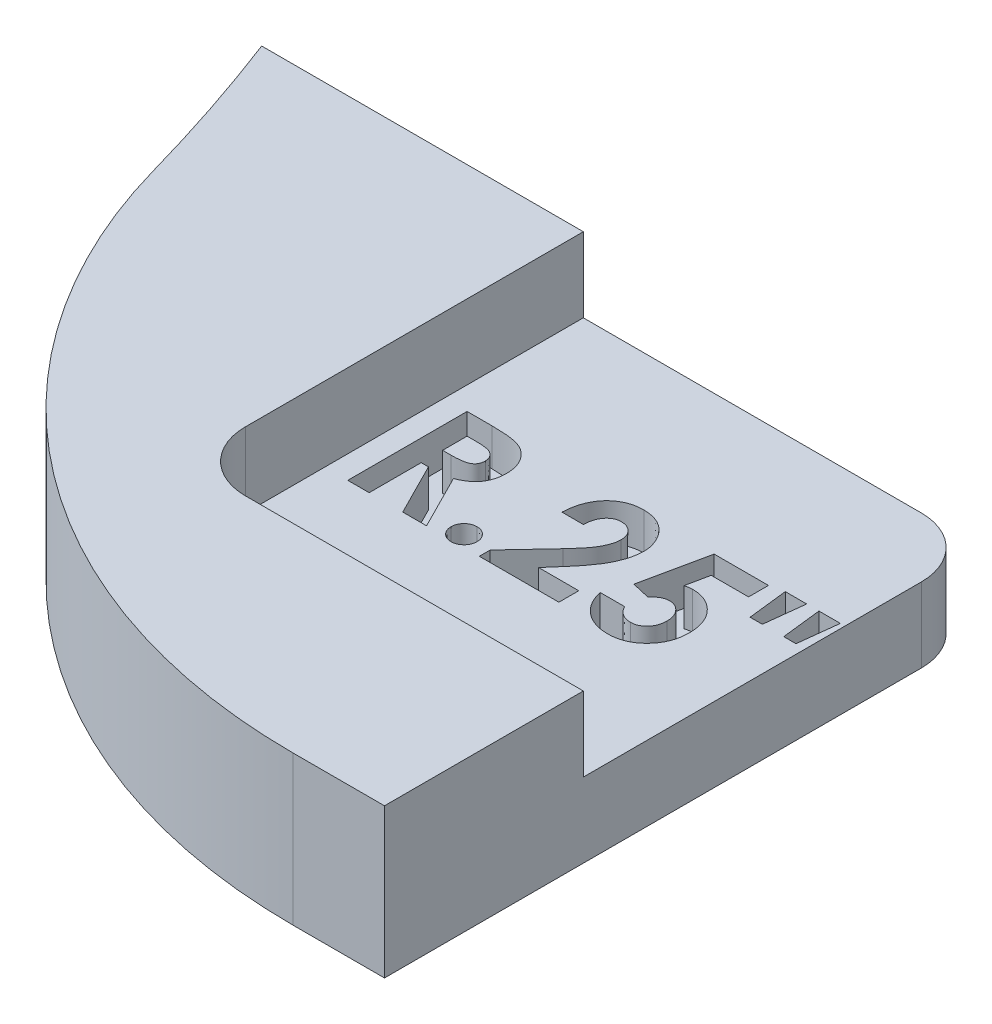
SolidWorks part; units mm, degrees
ref_plane "Front Plane" through (0, 0, 0) normal (0, 0, 1) x (1, 0, 0)
ref_plane "Top Plane" through (0, 0, 0) normal (0, 1, 0) x (1, 0, 0)
ref_plane "Right Plane" through (0, 0, 0) normal (1, 0, 0) x (0, 0, -1)
sketch "Sketch2" plane through (0, 0, 0) normal (0, 1, 0) x (1, 0, 0)
  line L0 (39.9034, 0) -> (66.5271, 0) construction
  line L4 (39.8718, 1.5875) -> (52.5718, 1.5875)
  line L5 (52.5718, 1.5875) -> (52.5718, 14.2875)
  line L6 (52.5718, 14.2875) -> (37.2579, 14.2875)
  arc A0 (39.8718, 1.5875) -> (37.2579, 14.2875) centre (0, 0) ccw
  arc A1 (37.2579, 14.2875) -> (-39.9034, 0) centre (0, 0) ccw construction
  arc A2 (-39.9034, 0) -> (39.9034, 0) centre (0, 0) ccw construction
  arc A3 (39.9034, 0) -> (39.8718, 1.5875) centre (0, 0) ccw construction
  point P6 (45.8249, 5.2638)
  point P7 (37.9479, 12.3384)
  point P10 (43.0639, 5.8161)
extrude "Boss-Extrude1" add sketch "Sketch2" along normal mid plane 3.175
fillet "Fillet1" radius 12.7 1 edges at (39.8718, 0, -1.5875)
sketch "Sketch3" plane through (0, 1.5875, 0) normal (0, 1, 0) x (1, 0, 0)
  line L1 (52.5718, 14.2875) -> (44.1051, 14.2875)
  line L2 (52.5718, 14.2875) -> (52.5718, 5.8208)
  line L3 (52.5718, 5.8208) -> (44.1051, 5.8208)
  line L4 (44.1051, 14.2875) -> (44.1051, 5.8208)
  dimension "D1" = 8.4667
extrude "Cut-Extrude1" cut sketch "Sketch3" against normal blind 1.5875
sketch "Sketch4" plane through (0, 0, 0) normal (0, 1, 0) x (1, 0, 0)
  line L0 (44.1051, 10.0542) -> (52.5718, 10.0542) construction
  line L1 (44.1051, 14.2875) -> (44.1051, 5.8208) construction
  line L2 (52.5718, 5.8208) -> (52.5718, 14.2875) construction
  line L3 (44.1051, 8.7842) -> (52.5718, 8.7842) construction
  text T0 "<b>R.25\"</b>\r\n<b> </b>" font "Century Gothic" height 2.54
  dimension "D1" = 1.27
extrude "Cut-Extrude2" cut sketch "Sketch4" against normal blind 0.7937
fillet "Fillet2" radius 1.27 2 edges at (44.1051, 0.7937, -5.8208) (52.5718, -0.7937, -14.2875)
equation "\"AIRFRAME_OD\"= 3.142in"
equation "\"AIRFRAME_ID\"= 3.00in"
equation "\"FLAT_T\"= 0.125in"
equation "\"NOSE_EXP_L\"= 3.5in"
equation "\"NOSE_SHOULDER_L\"= 5in"
equation "\"MAIN_L\"= 30in"
equation "\"RECO_COUP_L\"= 6in"
equation "\"RECO_SWITCH_L\"= 1.5in"
equation "\"DROGUE_L\"= 14in"
equation "\"ATS_FORE_COUP_L\"= 4in"
equation "\"ATS_AFT_COUP_L\"= 2.5in"
equation "\"LOWER_L\"= 16in"
equation "\"FIN_N\"= 4"
equation "\"CR_AFT_X\"= 0.5in"
equation "\"CR_FORE_X\"= 6in"
equation "\"D1@Sketch2\"=\"AIRFRAME_OD\""
equation "\"D2@Sketch2\"=\"FLAT_T\"/2"
equation "\"D1@Boss-Extrude1\"=\"FLAT_T\""
